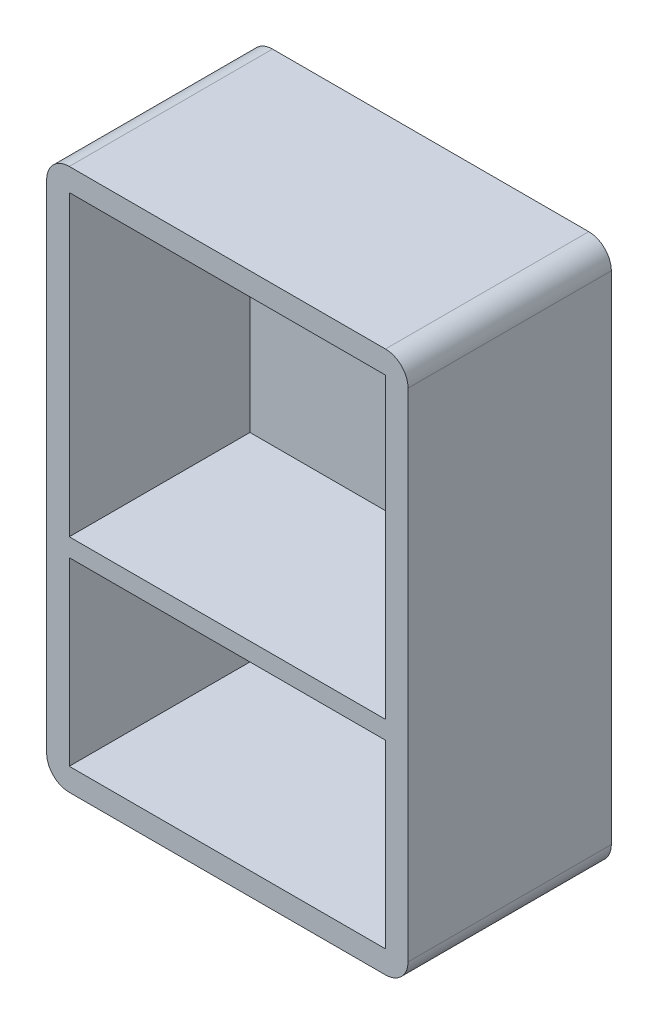
SolidWorks part; units mm, degrees
ref_plane "Front Plane" through (0, 0, 0) normal (0, 0, 1) x (1, 0, 0)
ref_plane "Top Plane" through (0, 0, 0) normal (0, 1, 0) x (1, 0, 0)
ref_plane "Right Plane" through (0, 0, 0) normal (1, 0, 0) x (0, 0, -1)
sketch "Sketch1" plane through (0, 0, 0) normal (0, 0, 1) x (1, 0, 0)
  line L1 (-40, 60) -> (40, 60)
  line L2 (-40, 60) -> (-40, -60)
  line L3 (-40, -60) -> (40, -60)
  line L4 (40, 60) -> (40, -60)
  line L5 (-40, 60) -> (40, -60) construction
  line L6 (-40, -60) -> (40, 60) construction
  point P0 (0, 0)
  dimension "D1" = 120
  dimension "D2" = 80
extrude "Boss-Extrude1" add sketch "Sketch1" along normal blind 5
sketch "Sketch2" plane through (0, 0, 5) normal (0, 0, 1) x (1, 0, 0)
  line L1 (-40, -60) -> (40, -60)
  line L2 (-40, -60) -> (-40, 60)
  line L3 (-40, 60) -> (40, 60)
  line L4 (40, -60) -> (40, 60)
  line L5 (-40, -60) -> (40, 60) construction
  line L6 (-40, 60) -> (40, -60) construction
  line L7 (-35, 55) -> (35, 55)
  line L8 (-35, 55) -> (-35, -11)
  line L9 (-35, -11) -> (35, -11)
  line L10 (35, 55) -> (35, -11)
  line L11 (-35, 55) -> (35, -11) construction
  line L12 (-35, -11) -> (35, 55) construction
  line L13 (-35, -55) -> (35, -55)
  line L14 (-35, -55) -> (-35, -15)
  line L15 (-35, -15) -> (35, -15)
  line L16 (35, -55) -> (35, -15)
  line L17 (-35, -55) -> (35, -15) construction
  line L18 (-35, -15) -> (35, -55) construction
  point P0 (0, 0)
  point P7 (0, 22)
  point P12 (0, -35)
  dimension "D1" = 5
  dimension "D2" = 5
  dimension "D3" = 5
  dimension "D4" = 5
  dimension "D5" = 5
  dimension "D6" = 5
  dimension "D7" = 40
  dimension "D8" = 4
extrude "Boss-Extrude2" add sketch "Sketch2" along normal blind 40
fillet "Fillet1" radius 5 4 edges at (-40, -60, 22.5) (40, -60, 22.5) (40, 60, 22.5) (-40, 60, 22.5)
